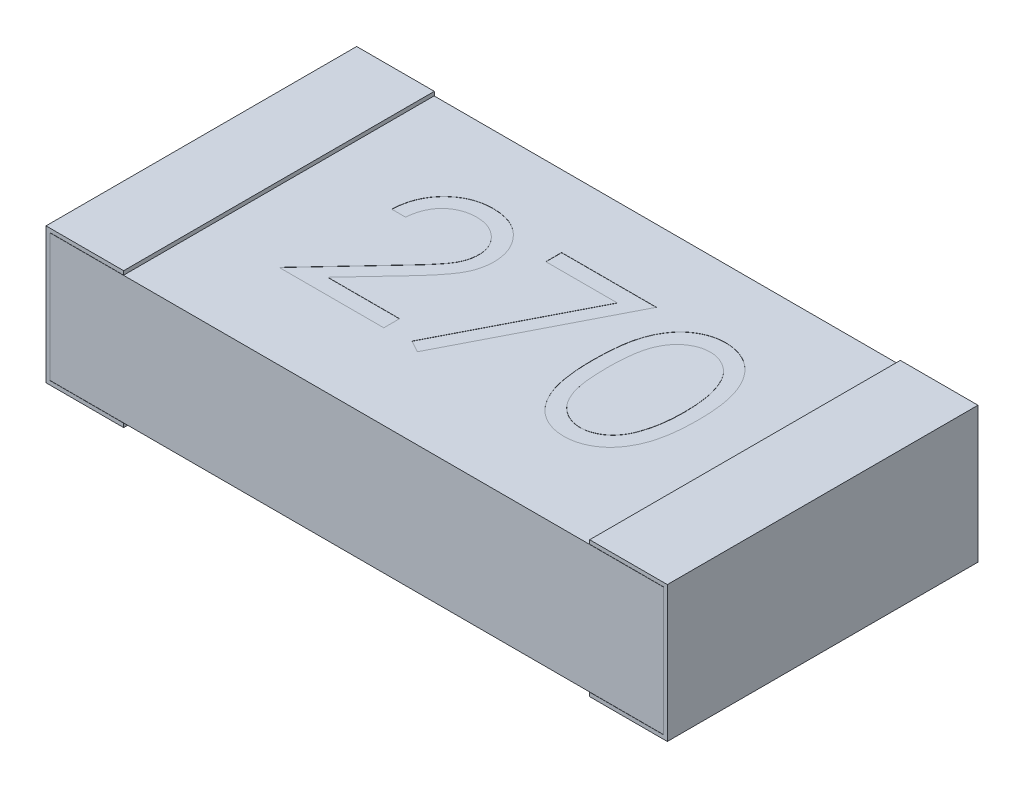
SolidWorks part; units mm, degrees
ref_plane "Front Plane" through (0, 0, 0) normal (0, 0, 1) x (1, 0, 0)
ref_plane "Top Plane" through (0, 0, 0) normal (0, 1, 0) x (1, 0, 0)
ref_plane "Right Plane" through (0, 0, 0) normal (1, 0, 0) x (0, 0, -1)
sketch "Sketch1" plane through (0, 0, 0) normal (0, 1, 0) x (1, 0, 0)
  line L1 (0, 0) -> (3.2, 0)
  line L2 (0, 0) -> (0, 1.6)
  line L3 (0, 1.6) -> (3.2, 1.6)
  line L4 (3.2, 0) -> (3.2, 1.6)
  dimension "D1" = 1.6
  dimension "D2" = 3.2
extrude "Boss-Extrude1" add sketch "Sketch1" along normal blind 0.7
sketch "Sketch2" plane through (0, 0, 0) normal (0, 0, 1) x (1, 0, 0)
  line L10 (0.4, 0.7) -> (0.4, 0.679)
  line L11 (2.8, 0.7) -> (2.8, 0.679)
  line L12 (0.4, 0.021) -> (0.4, 0)
  line L13 (2.8, 0.021) -> (2.8, 0)
  line L14 (3.179, 0.021) -> (3.179, 0.679)
  line L15 (0.021, 0.021) -> (3.179, 0.021)
  line L16 (0.021, 0.679) -> (0.021, 0.021)
  line L17 (3.179, 0.679) -> (0.021, 0.679)
  line L19 (0.4, 0.021) -> (2.8, 0.021)
  line L21 (2.8, 0.679) -> (0.4, 0.679)
  line L22 (0, 0) -> (3.2, 0)
  line L23 (3.2, 0) -> (3.2, 0.7)
  line L24 (3.2, 0.7) -> (0, 0.7)
  line L25 (0, 0.7) -> (0, 0)
  line L26 (0.4, 0) -> (2.8, 0)
  line L28 (2.8, 0.7) -> (0.4, 0.7)
  dimension "D1" = 0.021
  dimension "D2" = 0
extrude "Cut-Extrude1" cut sketch "Sketch2" against normal through all
sketch "Sketch5" plane through (0, 0, 0) normal (0, 0, 1) x (1, 0, 0)
  line L10 (0.38, 0.021) -> (0.021, 0.021)
  line L11 (0.021, 0.021) -> (0.021, 0.679)
  line L12 (0.021, 0.679) -> (0.4, 0.679)
  line L13 (0.38, 0.02) -> (0.4, 0.02)
  line L14 (0.38, 0.021) -> (0.38, 0.02)
  line L15 (0.38, 0.02) -> (0.02, 0.02)
  line L16 (0.02, 0.02) -> (0.02, 0.68)
  line L17 (0.02, 0.68) -> (0.4, 0.68)
  line L18 (2.8, 0.68) -> (2.8, 0.679)
  line L19 (0.38, 0.02) -> (0.02, 0.02)
  line L20 (0.02, 0.02) -> (0.02, 0.68)
  line L21 (0.02, 0.68) -> (0.4, 0.68)
  line L22 (0.4, 0.021) -> (0.4, 0) construction
  line L23 (0.38, 0.021) -> (0.4, 0.021)
  line L24 (0.4, 0.021) -> (0.4, 0.02)
  line L25 (1.6, 0.679) -> (1.6, 0.021) construction
  line L26 (0.4, 0.679) -> (2.8, 0.679) construction
  line L27 (2.8, 0.021) -> (0.4, 0.021) construction
  line L28 (2.8, 0.021) -> (2.8, 0.02)
  line L29 (2.82, 0.021) -> (2.8, 0.021)
  line L30 (3.18, 0.68) -> (2.8, 0.68)
  line L31 (3.18, 0.02) -> (3.18, 0.68)
  line L32 (2.82, 0.02) -> (3.18, 0.02)
  line L34 (2.82, 0.02) -> (2.8, 0.02)
  line L35 (3.179, 0.679) -> (2.8, 0.679)
  line L36 (3.179, 0.021) -> (3.179, 0.679)
  line L37 (2.82, 0.021) -> (3.179, 0.021)
  line M6 (0.4, 0) -> (0.4, 0.021)
  line M14 (0.4, 0.679) -> (0.4, 0.7)
  dimension "D1" = 0.02
  dimension "D2" = 0.001
extrude "Cut-Extrude2" cut sketch "Sketch5" against normal through all contours L23 L10 L11 L12 L21 L20 L19 L13 M14 M6 | L35 L18 L30 L31 L32 L34 L28 L29 L37 L36
sketch "Sketch6" plane through (0, 0.679, 0) normal (0, 1, 0) x (1, 0, 0)
  text T0 "270" font "Century Gothic" height in points 3
extrude "Cut-Extrude3" cut sketch "Sketch6" against normal blind 0.001
